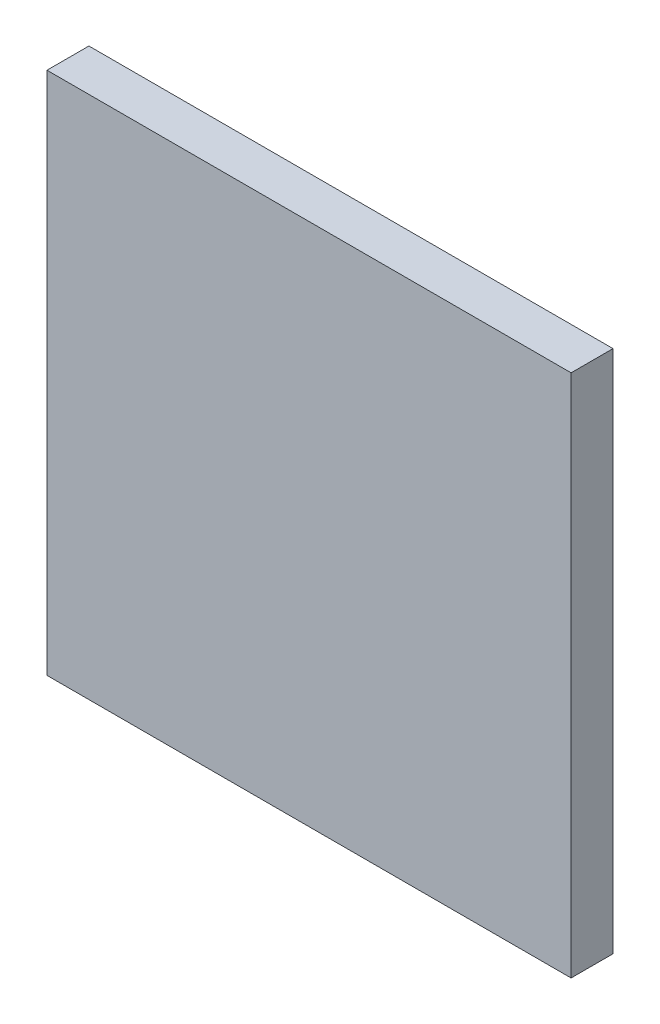
SolidWorks part; units mm, degrees
material "1060 Alloy"
ref_plane "Front Plane" through (0, 0, 0) normal (0, 0, 1) x (1, 0, 0)
ref_plane "Top Plane" through (0, 0, 0) normal (0, 1, 0) x (1, 0, 0)
ref_plane "Right Plane" through (0, 0, 0) normal (1, 0, 0) x (0, 0, -1)
sketch "Sketch1" plane through (0, 0, 0) normal (0, 0, 1) x (1, 0, 0)
  line L1 (0, 0) -> (50, 0)
  line L2 (0, 0) -> (0, 50)
  line L3 (0, 50) -> (50, 50)
  line L4 (50, 0) -> (50, 50)
  dimension "D1" = 50
  dimension "D2" = 50
extrude "Boss-Extrude1" add sketch "Sketch1" along normal blind 4
